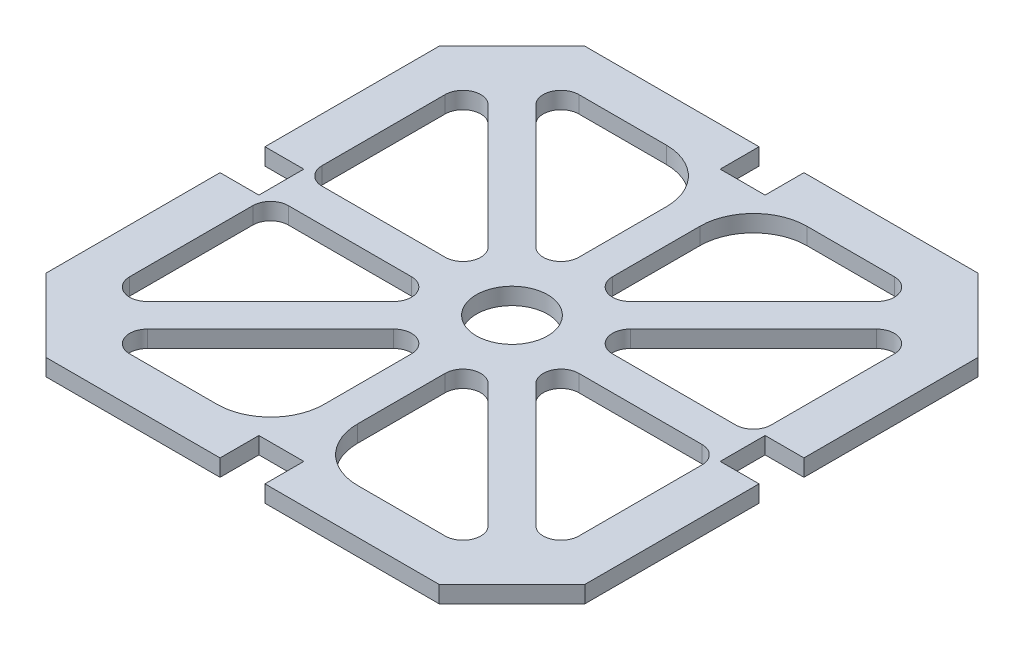
SolidWorks part; units mm, degrees
ref_plane "Front Plane" through (0, 0, 0) normal (0, 0, 1) x (1, 0, 0)
ref_plane "Top Plane" through (0, 0, 0) normal (0, 1, 0) x (1, 0, 0)
ref_plane "Right Plane" through (0, 0, 0) normal (1, 0, 0) x (0, 0, -1)
sketch "Sketch1" plane through (0, 0, 0) normal (0, 1, 0) x (1, 0, 0)
  line L0 (48, -4) -> (41.0806, -4)
  line L1 (41.0806, -4) -> (41.0806, 4)
  line L2 (41.0806, 4) -> (48, 4)
  line L3 (48, 4) -> (48, 35)
  line L4 (48, 35) -> (35, 48)
  line L5 (35, 48) -> (4, 48)
  line L6 (4, 48) -> (4, 41.0806)
  line L7 (4, 41.0806) -> (-4, 41.0806)
  line L8 (-4, 41.0806) -> (-4, 48)
  line L9 (-4, 48) -> (-35, 48)
  line L10 (-35, 48) -> (-48, 35)
  line L11 (-48, 35) -> (-48, 4)
  line L12 (-48, 4) -> (-41.0806, 4)
  line L13 (-30.3373, 34.5799) -> (-8.4201, 12.6627) construction
  line L14 (-41.0806, -4) -> (-48, -4)
  line L15 (-48, -4) -> (-48, -35)
  line L16 (-48, -35) -> (-35, -48)
  line L17 (-35, -48) -> (-4, -48)
  line L18 (-4, -48) -> (-4, -41.0806)
  line L19 (-4, -41.0806) -> (4, -41.0806)
  line L20 (4, -41.0806) -> (4, -48)
  line L21 (4, -48) -> (35, -48)
  line L22 (35, -48) -> (48, -35)
  line L23 (48, -35) -> (48, -4)
  line L24 (-36.9114, 0) -> (41.0806, 0) construction
  line L25 (0, 41.0806) -> (0, -41.0806) construction
  line L26 (-41.0806, 4) -> (-41.0806, -4)
  line L27 (-41.0806, -4) -> (-41.0806, -35) construction
  line L28 (-12.525, 40) -> (-28.0922, 40) construction
  line L29 (-3, 30.475) -> (-3, 14.9078) construction
  line L30 (3, 14.9078) -> (3, 30.475) construction
  line L31 (12.525, 40) -> (28.0922, 40) construction
  line L32 (30.3373, 34.5799) -> (8.4201, 12.6627) construction
  line L33 (12.6627, 8.4201) -> (34.5799, 30.3373) construction
  line L34 (36.825, 3) -> (14.9078, 3) construction
  line L35 (40, 28.0922) -> (40, 6.175) construction
  line L36 (40, -6.175) -> (40, -28.0922) construction
  line L37 (34.5799, -30.3373) -> (12.6627, -8.4201) construction
  line L38 (14.9078, -3) -> (36.825, -3) construction
  line L39 (30.3373, -34.5799) -> (8.4201, -12.6627) construction
  line L40 (3, -14.9078) -> (3, -30.475) construction
  line L41 (12.525, -40) -> (28.0922, -40) construction
  line L42 (-3, -14.9078) -> (-3, -30.475) construction
  line L43 (-30.3373, -34.5799) -> (-8.4201, -12.6627) construction
  line L44 (-12.525, -40) -> (-28.0922, -40) construction
  line L45 (-30.3373, 34.5799) -> (-8.4201, 12.6627)
  line L46 (-12.525, 40) -> (-28.0922, 40)
  line L47 (-3, 30.475) -> (-3, 14.9078)
  line L48 (3, 14.9078) -> (3, 30.475)
  line L49 (12.525, 40) -> (28.0922, 40)
  line L50 (30.3373, 34.5799) -> (8.4201, 12.6627)
  line L51 (12.6627, 8.4201) -> (34.5799, 30.3373)
  line L52 (36.825, 3) -> (14.9078, 3)
  line L53 (40, 28.0922) -> (40, 6.175)
  line L54 (40, -6.175) -> (40, -28.0922)
  line L55 (34.5799, -30.3373) -> (12.6627, -8.4201)
  line L56 (14.9078, -3) -> (36.825, -3)
  line L57 (30.3373, -34.5799) -> (8.4201, -12.6627)
  line L58 (3, -14.9078) -> (3, -30.475)
  line L59 (12.525, -40) -> (28.0922, -40)
  line L60 (-3, -14.9078) -> (-3, -30.475)
  line L61 (-30.3373, -34.5799) -> (-8.4201, -12.6627)
  line L62 (-12.525, -40) -> (-28.0922, -40)
  line L63 (-34.5799, -30.3373) -> (-12.6627, -8.4201) construction
  line L64 (-14.9078, -3) -> (-36.825, -3) construction
  line L65 (-40, -6.175) -> (-40, -28.0922) construction
  line L66 (-36.825, 3) -> (-14.9078, 3) construction
  line L67 (-40, 28.0922) -> (-40, 6.175) construction
  line L68 (-12.6627, 8.4201) -> (-34.5799, 30.3373) construction
  line L69 (-34.5799, -30.3373) -> (-12.6627, -8.4201)
  line L70 (-14.9078, -3) -> (-36.825, -3)
  line L71 (-40, -6.175) -> (-40, -28.0922)
  line L72 (-36.825, 3) -> (-14.9078, 3)
  line L73 (-40, 28.0922) -> (-40, 6.175)
  line L74 (-12.6627, 8.4201) -> (-34.5799, 30.3373)
  arc A0 (-28.0922, 40) -> (-30.3373, 34.5799) centre (-28.0922, 36.825) ccw construction
  arc A1 (-3, 30.475) -> (-12.525, 40) centre (-12.525, 30.475) ccw construction
  arc A2 (-8.4201, 12.6627) -> (-3, 14.9078) centre (-6.175, 14.9078) ccw construction
  arc A3 (3, 14.9078) -> (8.4201, 12.6627) centre (6.175, 14.9078) ccw construction
  arc A4 (12.525, 40) -> (3, 30.475) centre (12.525, 30.475) ccw construction
  arc A5 (30.3373, 34.5799) -> (28.0922, 40) centre (28.0922, 36.825) ccw construction
  circle A6 centre (0, 0) radius 6.35 construction
  arc A7 (12.6627, 8.4201) -> (14.9078, 3) centre (14.9078, 6.175) ccw construction
  arc A8 (36.825, 3) -> (40, 6.175) centre (36.825, 6.175) ccw construction
  arc A9 (40, 28.0922) -> (34.5799, 30.3373) centre (36.825, 28.0922) ccw construction
  arc A10 (40, -6.175) -> (36.825, -3) centre (36.825, -6.175) ccw construction
  arc A11 (34.5799, -30.3373) -> (40, -28.0922) centre (36.825, -28.0922) ccw construction
  arc A12 (14.9078, -3) -> (12.6627, -8.4201) centre (14.9078, -6.175) ccw construction
  arc A13 (8.4201, -12.6627) -> (3, -14.9078) centre (6.175, -14.9078) ccw construction
  arc A14 (3, -30.475) -> (12.525, -40) centre (12.525, -30.475) ccw construction
  arc A15 (28.0922, -40) -> (30.3373, -34.5799) centre (28.0922, -36.825) ccw construction
  arc A16 (-3, -14.9078) -> (-8.4201, -12.6627) centre (-6.175, -14.9078) ccw construction
  arc A17 (-30.3373, -34.5799) -> (-28.0922, -40) centre (-28.0922, -36.825) ccw construction
  arc A18 (-12.525, -40) -> (-3, -30.475) centre (-12.525, -30.475) ccw construction
  arc A19 (-28.0922, 40) -> (-30.3373, 34.5799) centre (-28.0922, 36.825) ccw
  arc A20 (-3, 30.475) -> (-12.525, 40) centre (-12.525, 30.475) ccw
  arc A21 (-8.4201, 12.6627) -> (-3, 14.9078) centre (-6.175, 14.9078) ccw
  arc A22 (3, 14.9078) -> (8.4201, 12.6627) centre (6.175, 14.9078) ccw
  arc A23 (12.525, 40) -> (3, 30.475) centre (12.525, 30.475) ccw
  arc A24 (30.3373, 34.5799) -> (28.0922, 40) centre (28.0922, 36.825) ccw
  circle A25 centre (0, 0) radius 6.35
  arc A26 (12.6627, 8.4201) -> (14.9078, 3) centre (14.9078, 6.175) ccw
  arc A27 (36.825, 3) -> (40, 6.175) centre (36.825, 6.175) ccw
  arc A28 (40, 28.0922) -> (34.5799, 30.3373) centre (36.825, 28.0922) ccw
  arc A29 (40, -6.175) -> (36.825, -3) centre (36.825, -6.175) ccw
  arc A30 (34.5799, -30.3373) -> (40, -28.0922) centre (36.825, -28.0922) ccw
  arc A31 (14.9078, -3) -> (12.6627, -8.4201) centre (14.9078, -6.175) ccw
  arc A32 (8.4201, -12.6627) -> (3, -14.9078) centre (6.175, -14.9078) ccw
  arc A33 (3, -30.475) -> (12.525, -40) centre (12.525, -30.475) ccw
  arc A34 (28.0922, -40) -> (30.3373, -34.5799) centre (28.0922, -36.825) ccw
  arc A35 (-3, -14.9078) -> (-8.4201, -12.6627) centre (-6.175, -14.9078) ccw
  arc A36 (-30.3373, -34.5799) -> (-28.0922, -40) centre (-28.0922, -36.825) ccw
  arc A37 (-12.525, -40) -> (-3, -30.475) centre (-12.525, -30.475) ccw
  arc A38 (-12.6627, -8.4201) -> (-14.9078, -3) centre (-14.9078, -6.175) ccw construction
  arc A39 (-36.825, -3) -> (-40, -6.175) centre (-36.825, -6.175) ccw construction
  arc A40 (-40, -28.0922) -> (-34.5799, -30.3373) centre (-36.825, -28.0922) ccw construction
  arc A41 (-14.9078, 3) -> (-12.6627, 8.4201) centre (-14.9078, 6.175) ccw construction
  arc A42 (-40, 6.175) -> (-36.825, 3) centre (-36.825, 6.175) ccw construction
  arc A43 (-34.5799, 30.3373) -> (-40, 28.0922) centre (-36.825, 28.0922) ccw construction
  arc A44 (-12.6627, -8.4201) -> (-14.9078, -3) centre (-14.9078, -6.175) ccw
  arc A45 (-36.825, -3) -> (-40, -6.175) centre (-36.825, -6.175) ccw
  arc A46 (-40, -28.0922) -> (-34.5799, -30.3373) centre (-36.825, -28.0922) ccw
  arc A47 (-14.9078, 3) -> (-12.6627, 8.4201) centre (-14.9078, 6.175) ccw
  arc A48 (-40, 6.175) -> (-36.825, 3) centre (-36.825, 6.175) ccw
  arc A49 (-34.5799, 30.3373) -> (-40, 28.0922) centre (-36.825, 28.0922) ccw
  dimension "D1" = 6.9194
  dimension "D3" = 6.9194
extrude "Boss-Extrude1" add sketch "Sketch1" along normal blind 3
